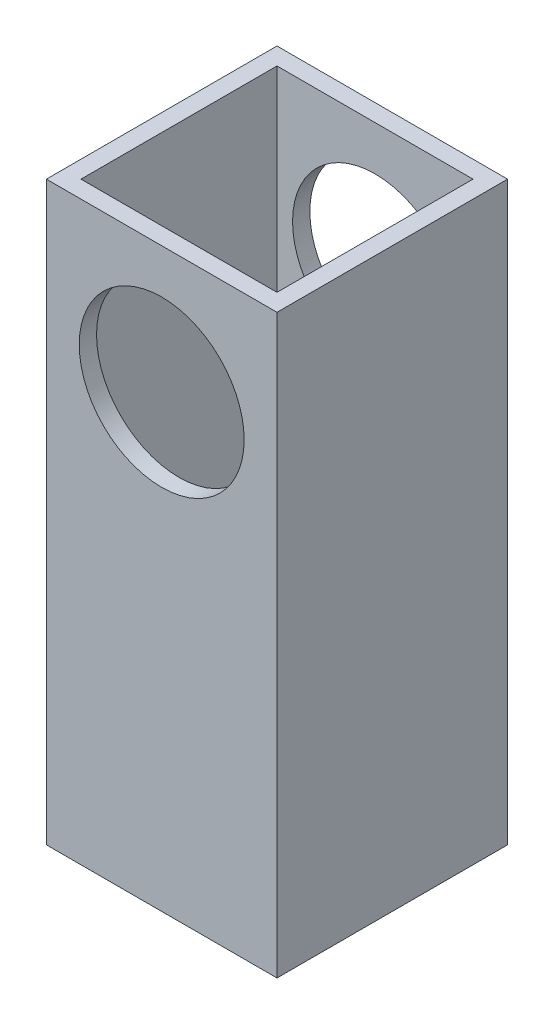
SolidWorks part; units mm, degrees
ref_plane "Front Plane" through (0, 0, 0) normal (0, 0, 1) x (1, 0, 0)
ref_plane "Top Plane" through (0, 0, 0) normal (0, 1, 0) x (1, 0, 0)
ref_plane "Right Plane" through (0, 0, 0) normal (1, 0, 0) x (0, 0, -1)
sketch "Sketch1" plane through (0, 0, 0) normal (0, 0, 1) x (1, 0, 0)
  line L1 (20, -50) -> (-20, -50)
  line L2 (20, -50) -> (20, 50)
  line L3 (20, 50) -> (-20, 50)
  line L4 (-20, -50) -> (-20, 50)
  line L5 (20, -50) -> (-20, 50) construction
  line L6 (20, 50) -> (-20, -50) construction
  point P0 (0, 0)
  dimension "D1" = 40
  dimension "D2" = 100
extrude "Boss-Extrude2" add sketch "Sketch1" along normal blind 40
sketch "Sketch2" plane through (0, 0, 40) normal (0, 0, 1) x (1, 0, 0)
  circle A0 centre (0, 28) radius 14.3
  point P2 (0, 28.7641)
  dimension "D1" = 28.6
  dimension "D2" = 28
extrude "Cut-Extrude1" cut sketch "Sketch2" against normal through all
sketch "Sketch3" plane through (0, 50, 0) normal (0, 1, 0) x (1, 0, 0)
  line L8 (17, -3) -> (-17, -3)
  line L9 (-17, -3) -> (-17, -37)
  line L10 (-17, -37) -> (17, -37)
  line L11 (17, -37) -> (17, -3)
  line L12 (17, -3) -> (-17, -3)
  line L13 (-17, -3) -> (-17, -37)
  line L14 (-17, -37) -> (17, -37)
  line L15 (17, -37) -> (17, -3)
  dimension "D1" = 3
extrude "Cut-Extrude2" cut sketch "Sketch3" against normal through all
